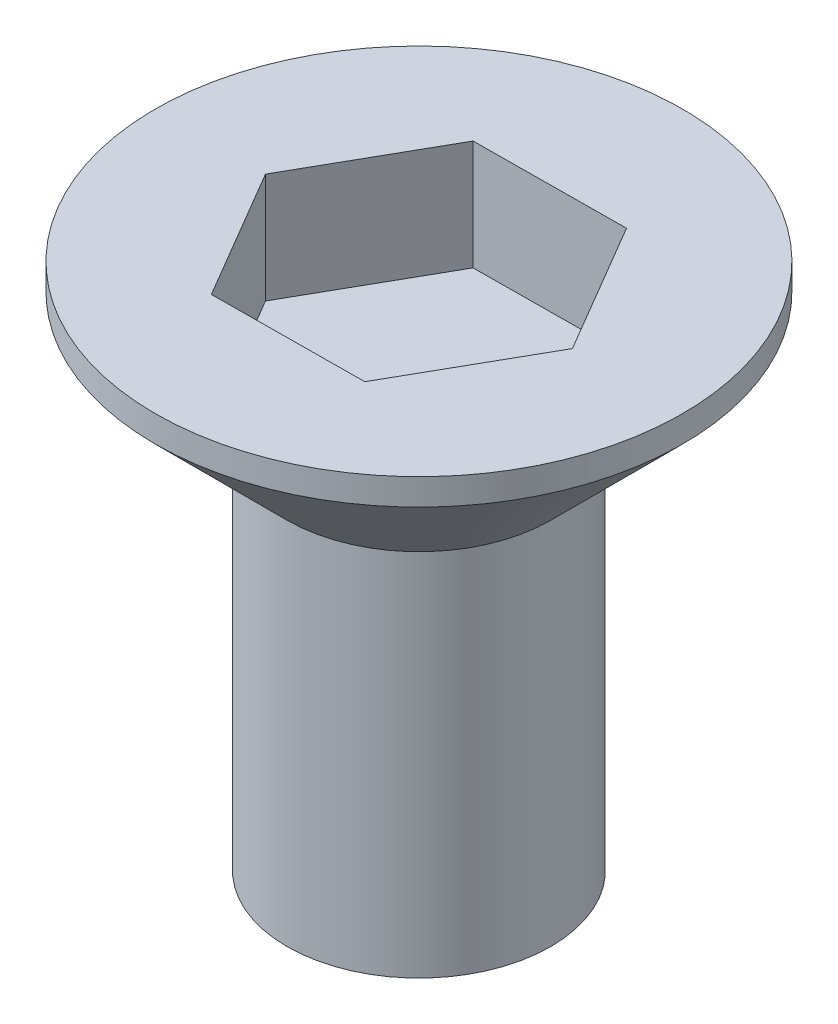
SolidWorks part; units mm, degrees
ref_plane "Спереди" through (0, 0, 0) normal (0, 0, 1) x (1, 0, 0)
ref_plane "Сверху" through (0, 0, 0) normal (0, 1, 0) x (1, 0, 0)
ref_plane "Справа" through (0, 0, 0) normal (1, 0, 0) x (0, 0, -1)
sketch "Эскиз1" plane through (0, 0, 0) normal (0, 0, 1) x (1, 0, 0)
  line L0 (0, 0) -> (3, 0)
  line L1 (3, 0) -> (3, 8.4)
  line L2 (3, 8.4) -> (6, 11.4)
  line L3 (6, 11.4) -> (6, 12)
  line L4 (6, 12) -> (0, 12)
  line L5 (0, 68.6446) -> (0, -29.1082) construction
  line L6 (0, 0) -> (0, 12)
  point P9 (0, 0)
revolve "Повернуть1" add sketch "Эскиз1" angle 360 about L5
sketch "Эскиз2" plane through (0, 12, 0) normal (0, 1, 0) x (1, 0, 0)
  line L1 (1.7553, -2.9865) -> (3.464, 0.0269)
  line L2 (3.464, 0.0269) -> (1.7087, 3.0133)
  line L3 (1.7087, 3.0133) -> (-1.7553, 2.9865)
  line L4 (-1.7553, 2.9865) -> (-3.464, -0.0269)
  line L5 (-3.464, -0.0269) -> (-1.7087, -3.0133)
  line L6 (-1.7087, -3.0133) -> (1.7553, -2.9865)
  circle A0 centre (0, 0) radius 3 construction
extrude "Вырез-Вытянуть1" cut sketch "Эскиз2" against normal blind 2.5
